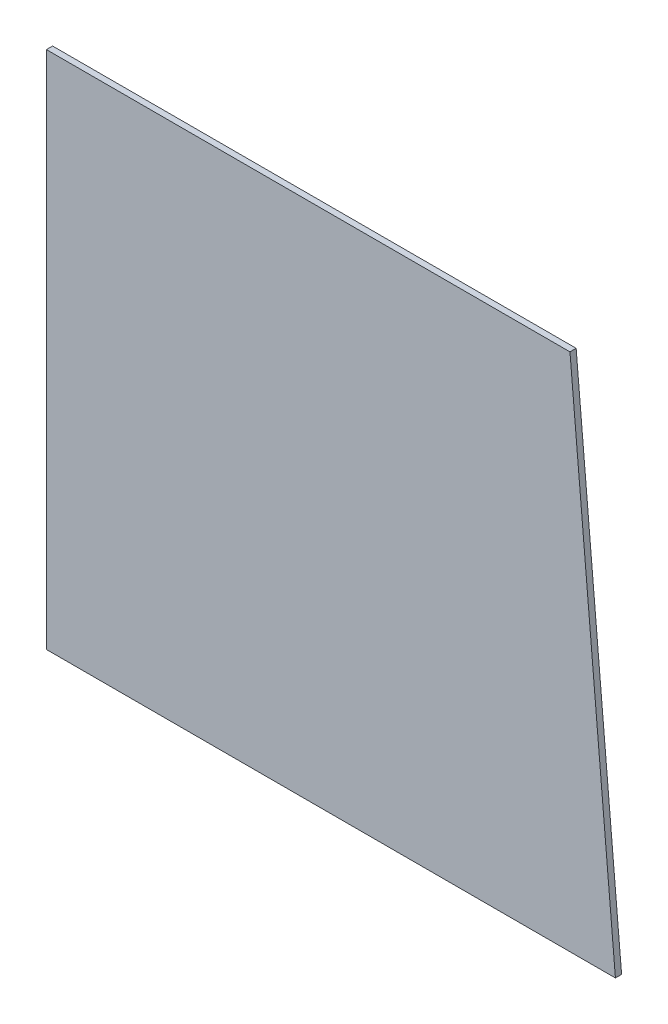
SolidWorks part; units mm, degrees
ref_plane "Front Plane" through (0, 0, 0) normal (0, 0, 1) x (1, 0, 0)
ref_plane "Top Plane" through (0, 0, 0) normal (0, 1, 0) x (1, 0, 0)
ref_plane "Right Plane" through (0, 0, 0) normal (1, 0, 0) x (0, 0, -1)
sketch "Sketch1" plane through (0, 0, 0) normal (0, 0, 1) x (1, 0, 0)
  line L0 (146.05, 0) -> (134.3834, 133.35)
  line L1 (0, 0) -> (146.05, 0)
  line L2 (0, 0) -> (0, 133.35)
  line L3 (0, 133.35) -> (134.3834, 133.35)
  dimension "D1" = 146.05
  dimension "D2" = 133.35
  dimension "D3" = 5
extrude "Boss-Extrude2" add sketch "Sketch1" along normal blind 1.5875
